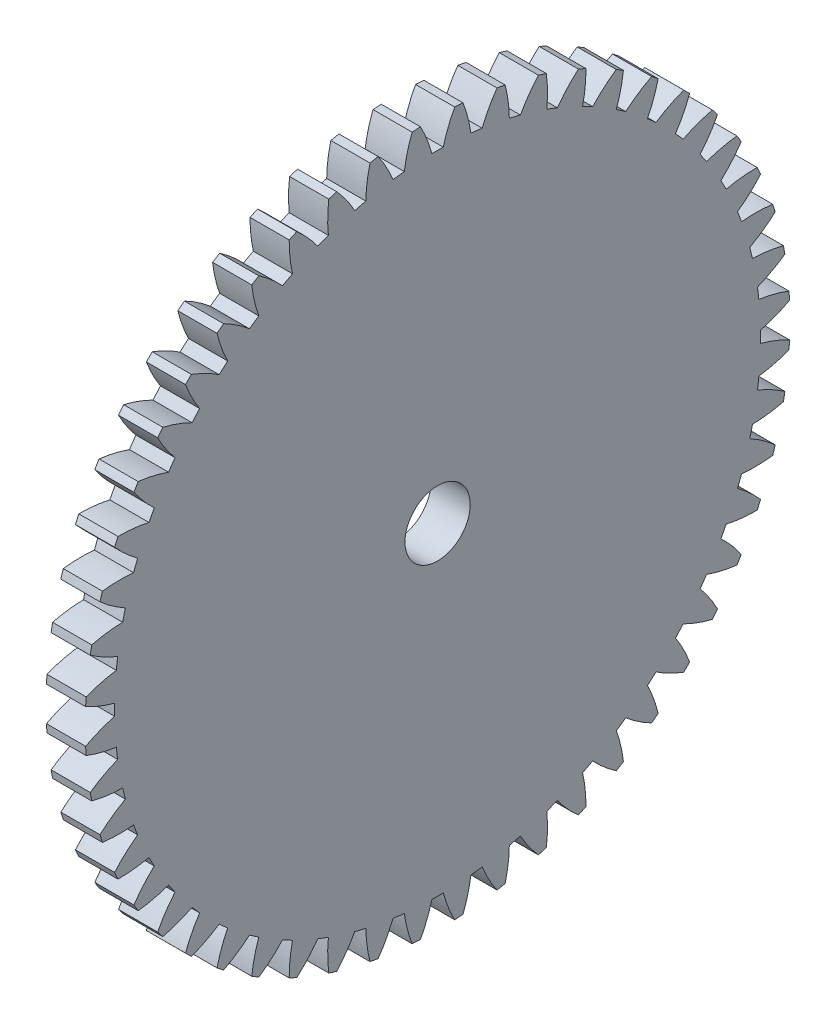
SolidWorks part; units mm, degrees
ref_plane "Plane1" through (0, 0, 0) normal (0, 0, 1) x (1, 0, 0)
ref_plane "Plane2" through (0, 0, 0) normal (0, 1, 0) x (1, 0, 0)
ref_plane "Plane3" through (0, 0, 0) normal (1, 0, 0) x (0, 0, -1)
sketch "HoldingSke" plane through (0, 0, 0) normal (0, 1, 0) x (1, 0, 0)
  line L0 (0, 0) -> (0.6157, -0.788)
  line L1 (-15, 0) -> (100, 0) construction
  line L2 (0, 0) -> (-2.1039, 2.3779)
  line L3 (0, 0) -> (-11.863, 4.5341)
  line L4 (0, 0) -> (5.3169, 6.8053)
  line L5 (0, 0) -> (-46.8476, -17.4728)
  line L6 (0, 0) -> (-2.4869, -1.6779)
  line L7 (-2.1039, 2.3779) -> (8.6586, 51.2059)
  line L8 (-76.2, 54.61) -> (-75.3, 54.61)
  line L9 (-71.009, 38.7566) -> (-53.1078, 45.2721)
  line L10 (-76.2, 71.12) -> (104.1128, 71.12)
  line L11 (0, 0) -> (-3, 0)
  line L12 (-76.2, 101.6) -> (-76.162, 101.6)
  line L13 (24.9733, 27.94) -> (52.9518, 28.4284)
  line L14 (24.9733, 27.94) -> (24.9743, 27.94)
  line L15 (24.9733, 27.94) -> (100.4006, 29.5858)
  line L16 (-63.627, -1) -> (-12.827, -1)
  circle A0 centre (0, 0) radius 2.5
  circle A1 centre (0, 0) radius 24.749
  circle A2 centre (0, 0) radius 37.5
  circle A3 centre (0, 0) radius 2.5
  dimension "MHD" = 49.498
  dimension "Hub_dia" = 75
  dimension "Bore" = 5
  dimension "MBD" = 5
  dimension "Num_teeth" = 52
  dimension "Pitch_radius" = 180.3128
  dimension "Pitch" = 1
  dimension "Width" = 3
  dimension "Overall_len" = 50
  dimension "Show_teeth" = 52
  dimension "Thickness" = 3
  dimension "OAL" = 50.0001
  dimension "T_dim" = 0.9
  dimension "Ap" = 20
  dimension "H" = 19.05
  dimension "Backlash" = 0.038
  dimension "Addendum_fac" = 1
  dimension "Dedendum_fac" = 1.25
  dimension "Clearance_fac" = 0.25
  dimension "Dedendum_add" = 0.001
  dimension "Module" = 1
sketch "BasProSke" plane through (0, 0, 0) normal (0, 1, 0) x (1, 0, 0)
  line L0 (-10, 0) -> (60, 0) construction
  line L1 (0, 0) -> (0, 27)
  line L2 (0, 0) -> (3, 0)
  line L3 (3, 0) -> (3, 27)
  line L4 (3, 27) -> (0, 27)
  dimension "Diameter" = 54
  dimension "Thickness" = 3
revolve "Base-Revolve" add sketch "BasProSke" angle 360 about L0
sketch "TooCutSke" plane through (0, 0, 0) normal (1, 0, 0) x (0, 0, -1)
  line L1 (0, 0) -> (0, 107) construction
  line L2 (0, 0) -> (-0.8518, 25.986) construction
  line L3 (0, 0) -> (-3.1385, 51.8853) construction
  line L4 (-0.8518, 25.986) -> (-1.5692, 25.9426) construction
  arc A0 (0.4359, 24.7452) -> (-0.4359, 24.7452) centre (0, 0) ccw
  arc A1 (1.3256, 26.9929) -> (-1.3256, 26.9929) centre (0, 0) ccw
  circle A2 centre (0, 0) radius 26 construction
  circle A3 centre (0, 0) radius 24.432 construction
  arc A4 (-0.4359, 24.7452) -> (-1.3256, 26.9929) centre (-10.4854, 22.0676) ccw
  arc A5 (1.3256, 26.9929) -> (0.4359, 24.7452) centre (10.4854, 22.0676) ccw
  dimension "Root_dia" = 49.498
  dimension "Overcut_dia" = 54.0508
  dimension "Pitch_dia" = 52
  dimension "Base_dia" = 48.864
  dimension "Flank_rad" = 10.4
  dimension "Half_ang" = 3.462
  dimension "Half_CT" = 0.7188
extrude "ToothCut" cut sketch "TooCutSke" along normal through all
fillet "Breaks" [suppressed] radius 0.02
fillet "RootFillets" [suppressed] radius 0.251
pattern_circular "TeethCuts" count 52 every 6.923 about axis through (-10, 0, 0) along (1, 0, 0) of "ToothCut", "RootFillets", "Breaks"
sketch "HubNeaOneSke" plane through (0, 0, 0) normal (-1, 0, 0) x (0, 0, 1)
  circle A0 centre (0, 0) radius 24.749
  dimension "Diameter" = 49.498
extrude "HubNearOne" [suppressed] add sketch "HubNeaOneSke" along normal blind 47.0001
sketch "HubNeaBotSke" plane through (0, 0, 0) normal (-1, 0, 0) x (0, 0, 1)
  circle A0 centre (0, 0) radius 24.749
  dimension "Diameter" = 49.498
extrude "HubNearBoth" [suppressed] add sketch "HubNeaBotSke" along normal blind 23.5
ref_plane "FarPln" through (3, 0, 0) normal (1, 0, 0) x (0, 0, -1)
sketch "HubFarSke" plane through (3, 0, 0) normal (1, 0, 0) x (0, 0, -1)
  circle A0 centre (0, 0) radius 24.749
  dimension "Diameter" = 49.498
extrude "HubFar" [suppressed] add sketch "HubFarSke" along normal blind 23.5
sketch "BorSke" plane through (0, 0, 0) normal (1, 0, 0) x (0, 0, -1)
  circle A0 centre (0, 0) radius 2.5
  dimension "Diameter" = 5
extrude "Bore" cut sketch "BorSke" along normal mid plane 100.0001
sketch "KeySke" plane through (0, 0, 0) normal (1, 0, 0) x (0, 0, -1)
  line L0 (-1, 0) -> (-1, 3.4)
  line L1 (-1, 3.4) -> (1, 3.4)
  line L2 (1, 3.4) -> (1, 0)
  line L3 (0, 0) -> (0, 34) construction
  line L4 (-1, 0) -> (1, 0)
  dimension "Offset" = 3.4
  dimension "Width" = 2
extrude "Keyway" [suppressed] cut sketch "KeySke" along normal mid plane 100.0001
pattern_circular "Keyway2" [suppressed] count 2 every 90 about axis through (-10, 0, 0) along (1, 0, 0)
equation "' \"Module@HoldingSke\" = 6.35"
equation "' \"Num_teeth@HoldingSke\" = 12"
equation "' \"Ap@HoldingSke\" =  20"
equation "' \"Width@HoldingSke\" = 0.5 * 25.4"
equation "' \"Hub_dia@HoldingSke\"= 1 * 25.4"
equation "' \"Overall_len@HoldingSke\" = 1.0 * 25.4"
equation "' \"Bore@HoldingSke\" = 0.75 * 25.4"
equation "' \"T_dim@HoldingSke\" = 0.1 * 25.4"
equation "' \"Width@KeySke\" = 0.25 * 25.4"
equation "' \"Show_teeth@HoldingSke\" = 13"
equation "' \"Backlash@HoldingSke\" = 0.009 * 25.4"
equation "' \"Addendum_fac@HoldingSke\" = 1.0"
equation "' \"Dedendum_fac@HoldingSke\" = 1.25"
equation "' \"Dedendum_add@HoldingSke\" = 0.00005 * 25.4"
equation "' \"Clearance_fac@HoldingSke\" = 0.25"
equation "\"Pitch@HoldingSke\" = 1 / \"Module@HoldingSke\""
equation "\"Overcut_dia@TooCutSke\" = (\"Num_teeth@HoldingSke\" + 2 * \"Addendum_fac@HoldingSke\") / \"Pitch@HoldingSke\" + 0.002 * 25.4"
equation "\"Pitch_dia@TooCutSke\" = \"Num_teeth@HoldingSke\" / \"Pitch@HoldingSke\""
equation "\"Base_dia@TooCutSke\" = \"Num_teeth@HoldingSke\" / \"Pitch@HoldingSke\" * cos((\"Ap@HoldingSke\"  * 3.14159265 / 180))"
equation "\"Root_dia@TooCutSke\" = (\"Num_teeth@HoldingSke\" + 2) / \"Pitch@HoldingSke\" - 2 * (\"Addendum_fac@HoldingSke\" + \"Dedendum_fac@HoldingSke\") / \"Pitch@HoldingSke\" - \"Dedendum_add@HoldingSke\" * 2"
equation "\"Half_ang@TooCutSke\" = 180 / \"Num_teeth@HoldingSke\""
equation "\"Half_CT@TooCutSke\" = \"Num_teeth@HoldingSke\" / \"Pitch@HoldingSke\" * sin((3.14159265 / 2 / \"Num_teeth@HoldingSke\")) / 2 - 7 * \"Backlash@HoldingSke\" / 4"
equation "\"Flank_rad@TooCutSke\" = \"Num_teeth@HoldingSke\" / \"Pitch@HoldingSke\" / 5"
equation "\"Radius@RootFillets\" = \"Clearance_fac@HoldingSke\" / \"Pitch@HoldingSke\" + \"Dedendum_add@HoldingSke\""
equation "\"Break_rad@Breaks\" = 0.02 / \"Pitch@HoldingSke\""
equation "\"Thickness@HoldingSke\" = \"Width@HoldingSke\""
equation "\"OAL@HoldingSke\" = \"Thickness@HoldingSke\""
equation "\"MHD@HoldingSke\" = (\"Num_teeth@HoldingSke\" + 2) / \"Pitch@HoldingSke\" - 2 * (\"Addendum_fac@HoldingSke\" + \"Dedendum_fac@HoldingSke\")  / \"Pitch@HoldingSke\" - \"Dedendum_add@HoldingSke\" * 2"
equation "\"MBD@HoldingSke\" = (\"Num_teeth@HoldingSke\" + 2) / \"Pitch@HoldingSke\" - 2 * (\"Addendum_fac@HoldingSke\" + \"Dedendum_fac@HoldingSke\")  / \"Pitch@HoldingSke\" - \"Dedendum_add@HoldingSke\" * 2 - 0.002 * 25.4"
equation "\"MHD@HoldingSke\" = ((sgn( \"MHD@HoldingSke\" - \"Hub_dia@HoldingSke\" )-1)*( \"MHD@HoldingSke\" - \"Hub_dia@HoldingSke\" ))/-2+ \"Hub_dia@HoldingSke\""
equation "\"MBD@HoldingSke\" = ((sgn( \"MBD@HoldingSke\" - \"Bore@HoldingSke\" )-1)*( \"MBD@HoldingSke\" - \"Bore@HoldingSke\" ))/-2+ \"Bore@HoldingSke\""
equation "\"OAL@HoldingSke\" = ((sgn( \"OAL@HoldingSke\" - \"Overall_len@HoldingSke\" )+1)*( \"OAL@HoldingSke\" - \"Overall_len@HoldingSke\" ))/2 + \"Overall_len@HoldingSke\" + 0.000002 * 25.4"
equation "\"Num_teeth@TeethCuts\" = int( \"Show_teeth@HoldingSke\" ) + 1"
equation "\"Num_teeth@TeethCuts\" = ((sgn( \"Num_teeth@TeethCuts\" - \"Num_teeth@HoldingSke\" )-1)*( \"Num_teeth@TeethCuts\" - \"Num_teeth@HoldingSke\" ))/-2+ \"Num_teeth@HoldingSke\""
equation "\"Num_teeth@TeethCuts\" = ((sgn( \"Num_teeth@TeethCuts\" - 2.0)+1)*( \"Num_teeth@TeethCuts\" - 2.0))/2 +2.0"
equation "\"Angle@TeethCuts\" = 360.0 / \"Num_teeth@HoldingSke\""
equation "\"Diameter@BasProSke\" = (\"Num_teeth@HoldingSke\" + 2 * \"Addendum_fac@HoldingSke\") / \"Pitch@HoldingSke\""
equation "\"Thickness@BasProSke\"  = \"Thickness@HoldingSke\""
equation "' \"Fillet_rad@BasProSke\" =  \"Thickness@HoldingSke\" * 0.05"
equation "\"MHD@HoldingSke\" = ((sgn( \"MHD@HoldingSke\" - \"Root_dia@TooCutSke\" )-1)*( \"MHD@HoldingSke\" - \"Root_dia@TooCutSke\" ))/-2+ \"Root_dia@TooCutSke\""
equation "\"Diameter@HubNeaOneSke\" = \"MHD@HoldingSke\""
equation "\"Length@HubNearOne\" = \"OAL@HoldingSke\" - \"Thickness@BasProSke\""
equation "\"Diameter@HubNeaBotSke\" = \"MHD@HoldingSke\""
equation "\"Length@HubNearBoth\" = ( \"OAL@HoldingSke\" - \"Thickness@BasProSke\" ) / 2.0"
equation "\"Thickness@FarPln\" = \"Thickness@BasProSke\""
equation "\"Diameter@HubFarSke\" = \"MHD@HoldingSke\""
equation "\"Length@HubFar\" = ( \"OAL@HoldingSke\" - \"Thickness@BasProSke\" ) / 2.0"
equation "\"Diameter@BorSke\" = \"MBD@HoldingSke\""
equation "\"D1@Bore\" = \"OAL@HoldingSke\" * 2.0"
equation "\"D1@Keyway\" = \"OAL@HoldingSke\" * 2.0"
equation "\"Offset@KeySke\" = \"T_dim@HoldingSke\" + \"MBD@HoldingSke\" / 2.0"
